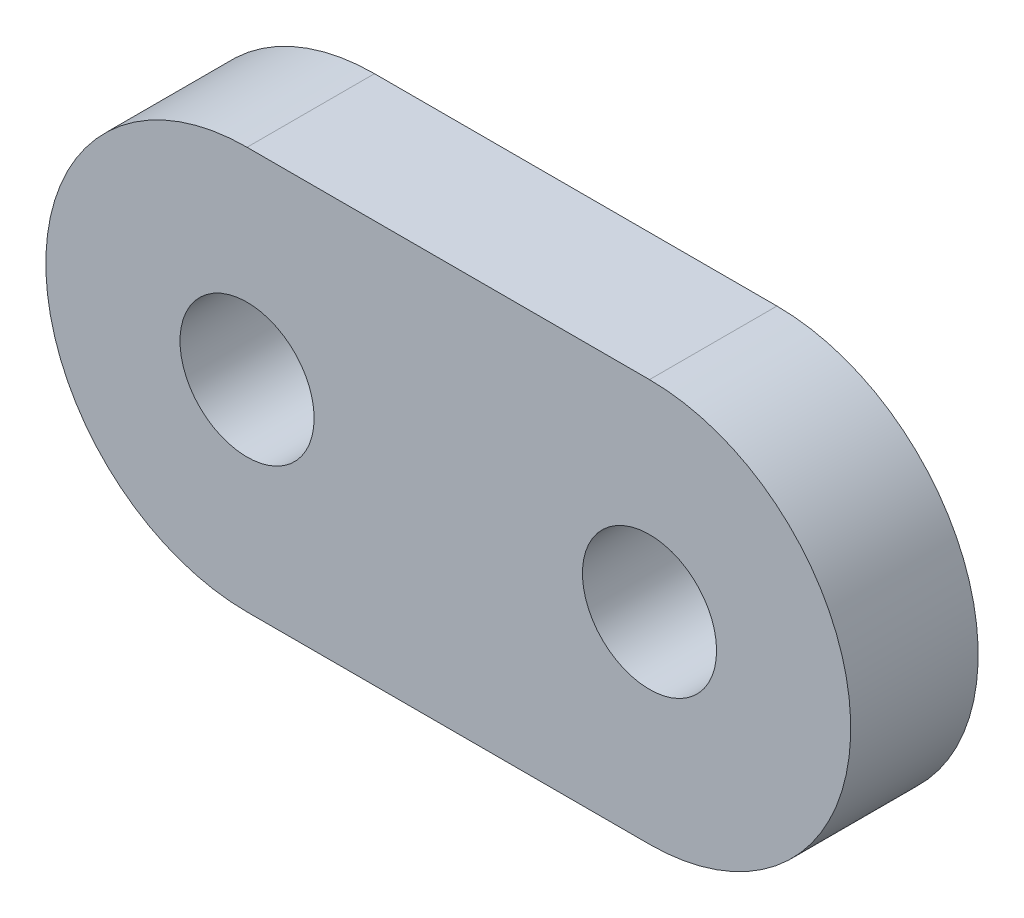
SolidWorks part; units mm, degrees
ref_plane "Front" through (0, 0, 0) normal (0, 0, 1) x (1, 0, 0)
ref_plane "Top" through (0, 0, 0) normal (0, 1, 0) x (1, 0, 0)
ref_plane "Right" through (0, 0, 0) normal (1, 0, 0) x (0, 0, -1)
sketch "草图1" plane through (0, 0, 0) normal (0, 0, 1) x (1, 0, 0)
  line L1 (0, -3) -> (6, -3)
  line L3 (0, 3) -> (6, 3)
  arc A0 (0, 3) -> (0, -3) centre (0, 0) ccw
  arc A1 (6, -3) -> (6, 3) centre (6, 0) ccw
  circle A2 centre (0, 0) radius 1
  circle A3 centre (6, 0) radius 1
  dimension "D1" = 6
  dimension "D2" = 6
  dimension "D4" = 2
  dimension "D5" = 2
  dimension "D3" = 6
extrude "凸台-拉伸1" add sketch "草图1" along normal blind 1.9
